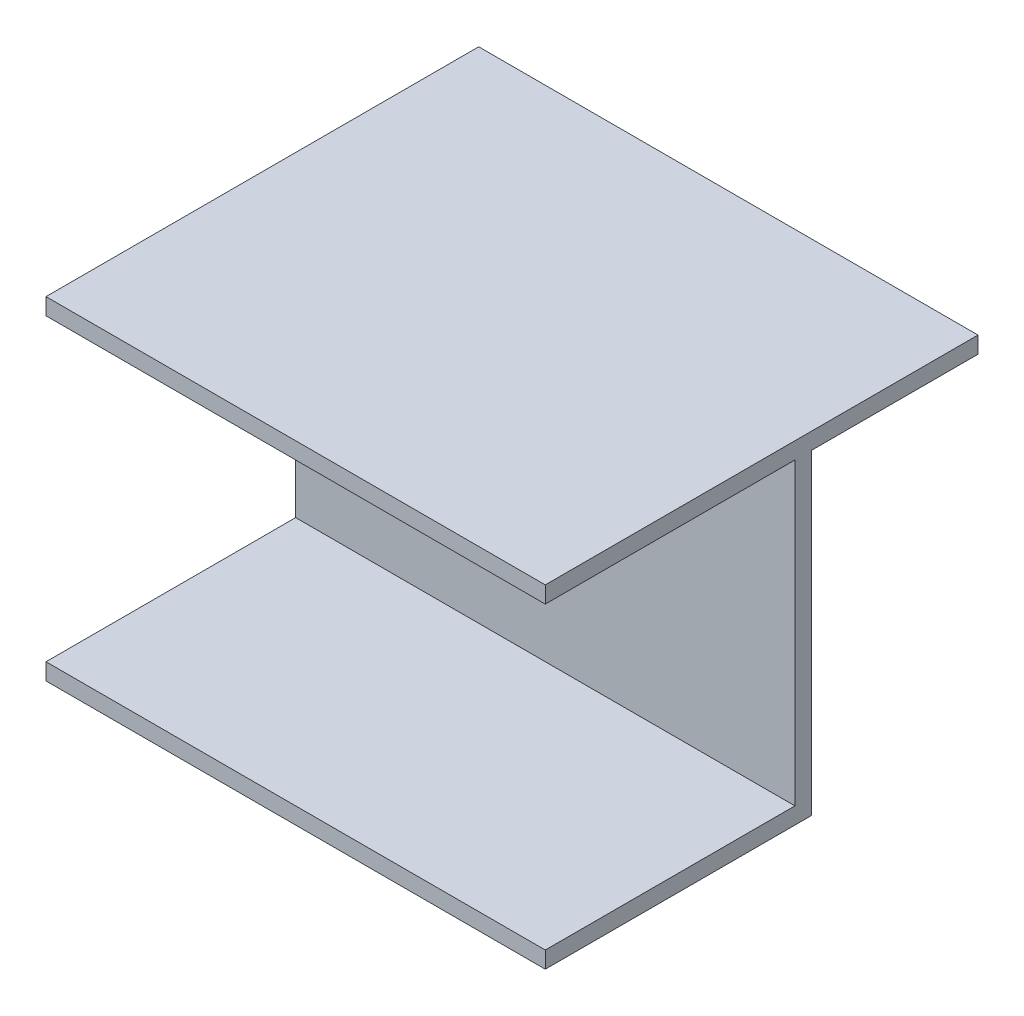
SolidWorks part; units mm, degrees
ref_plane "前视基准面" through (0, 0, 0) normal (0, 0, 1) x (1, 0, 0)
ref_plane "上视基准面" through (0, 0, 0) normal (0, 1, 0) x (1, 0, 0)
ref_plane "右视基准面" through (0, 0, 0) normal (1, 0, 0) x (0, 0, -1)
sketch "草图1" plane through (0, 0, 0) normal (0, 0, 1) x (1, 0, 0)
  line L1 (-31.5789, 13.4211) -> (28.4211, 13.4211)
  line L2 (-31.5789, 13.4211) -> (-31.5789, -26.5789)
  line L3 (-31.5789, -26.5789) -> (28.4211, -26.5789)
  line L4 (28.4211, 13.4211) -> (28.4211, -26.5789)
  dimension "D1" = 60
  dimension "D2" = 40
extrude "凸台-拉伸1" add sketch "草图1" along normal blind 2
sketch "草图2" plane through (0, 0, 2) normal (0, 0, 1) x (1, 0, 0)
  line L0 (28.4211, -26.5789) -> (28.4211, 13.4211) construction
  line L1 (-31.5789, 13.4211) -> (28.4211, 13.4211)
  line L2 (-31.5789, 13.4211) -> (-31.5789, 11.4211)
  line L3 (-31.5789, 11.4211) -> (28.4211, 11.4211)
  line L4 (28.4211, 13.4211) -> (28.4211, 11.4211)
  line L5 (-31.5789, -6.5789) -> (28.4211, -6.5789) construction
  line L6 (-31.5789, 13.4211) -> (-31.5789, -26.5789) construction
  line L7 (-31.5789, -24.5789) -> (28.4211, -24.5789)
  line L8 (28.4211, -26.5789) -> (28.4211, -24.5789)
  line L9 (-31.5789, -26.5789) -> (28.4211, -26.5789)
  line L10 (-31.5789, -26.5789) -> (-31.5789, -24.5789)
  dimension "D1" = 2
extrude "凸台-拉伸2" add sketch "草图2" along normal blind 30
sketch "草图3" plane through (0, 0, 0) normal (0, 0, -1) x (-1, 0, 0)
  line L0 (31.5789, 13.4211) -> (31.5789, -26.5789) construction
  line L1 (-28.4211, 13.4211) -> (31.5789, 13.4211)
  line L2 (-28.4211, 13.4211) -> (-28.4211, 11.4211)
  line L3 (-28.4211, 11.4211) -> (31.5789, 11.4211)
  line L4 (31.5789, 13.4211) -> (31.5789, 11.4211)
  dimension "D1" = 2
extrude "凸台-拉伸3" add sketch "草图3" along normal blind 20
